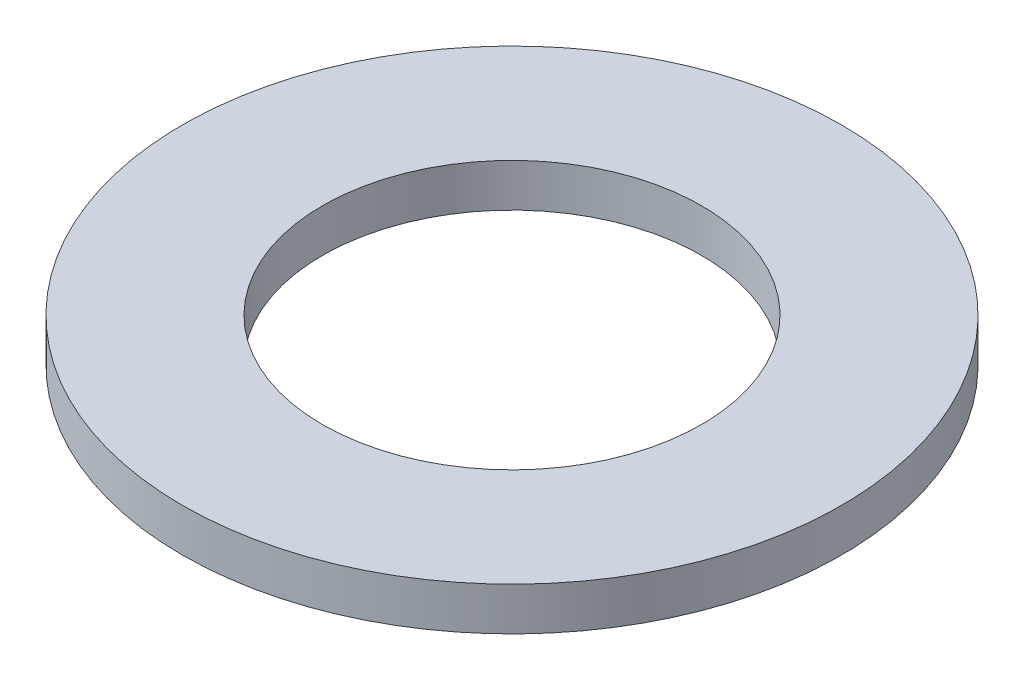
SolidWorks part; units mm, degrees
ref_plane "Front Plane" through (0, 0, 0) normal (0, 0, 1) x (1, 0, 0)
ref_plane "Top Plane" through (0, 0, 0) normal (0, 1, 0) x (1, 0, 0)
ref_plane "Right Plane" through (0, 0, 0) normal (1, 0, 0) x (0, 0, -1)
sketch "Sketch1" plane through (0, 0, 0) normal (0, 1, 0) x (1, 0, 0)
  circle A0 centre (0, 0) radius 1.9431
  dimension "OD" = 3.8862
extrude "Boss-Extrude1" add sketch "Sketch1" along normal blind 0.254
sketch "Sketch5" plane through (0, 0.254, 0) normal (0, 1, 0) x (-1, 0, 0)
  circle A0 centre (0, 0) radius 1.1176
  dimension "ID" = 2.2352
extrude "Cut-Extrude1" cut sketch "Sketch5" against normal through all
